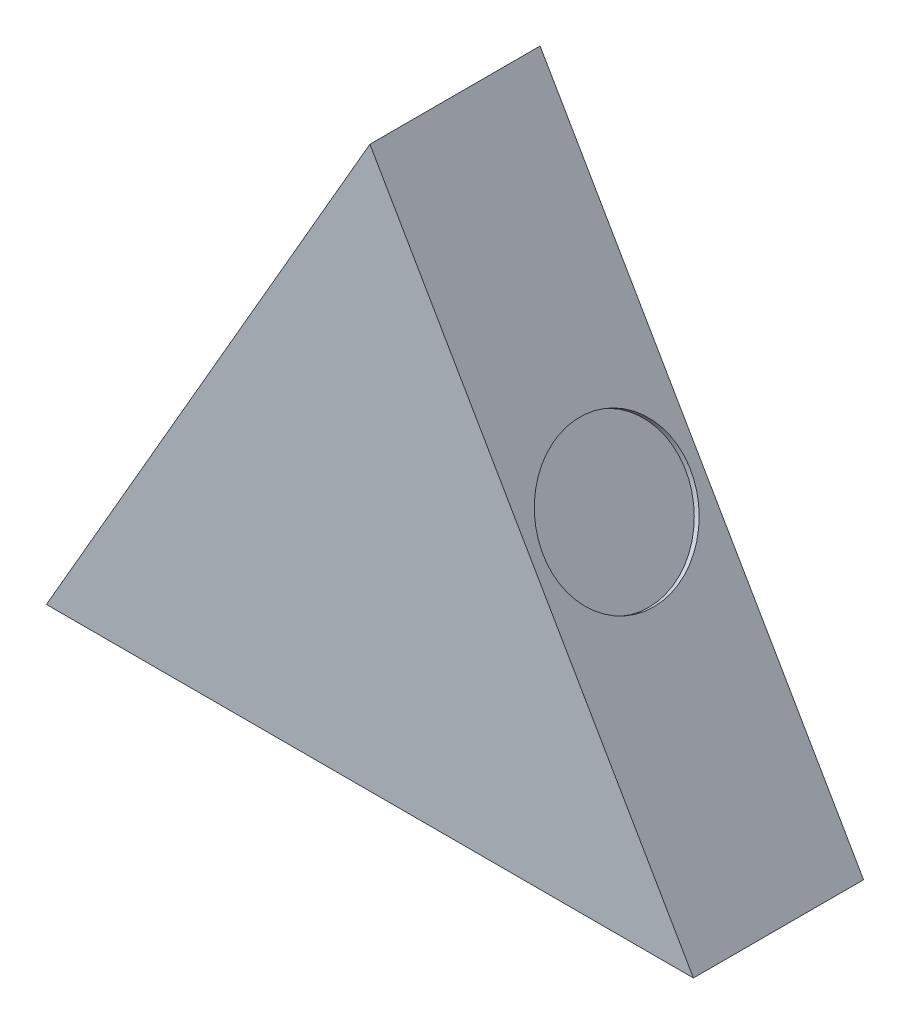
SolidWorks part; units mm, degrees
ref_plane "前视基准面" through (0, 0, 0) normal (0, 0, 1) x (1, 0, 0)
ref_plane "上视基准面" through (0, 0, 0) normal (0, 1, 0) x (1, 0, 0)
ref_plane "右视基准面" through (0, 0, 0) normal (1, 0, 0) x (0, 0, -1)
other "Configuration Table"
sketch "草图1" plane through (0, 0, 0) normal (0, 0, 1) x (1, 0, 0)
  line L0 (0, 0) -> (0, 24.6971) construction
  line L1 (0, 24.6971) -> (-28.5178, -24.6971)
  line L2 (-28.5178, -24.6971) -> (28.5178, -24.6971)
  line L3 (28.5178, -24.6971) -> (0, 24.6971)
  point P4 (0, 0)
extrude "凸台-拉伸2" add sketch "草图1" along normal blind 15
sketch "草图4" plane through (0, 0, 0) normal (0, 0, 1) x (1, 0, 0)
  line L0 (-13.4738, -3.563) -> (-13.4738, -20.063)
  line L1 (-10, -23.5368) -> (10, -23.5368)
  line L2 (13.4738, -3.563) -> (13.4738, -20.063)
  line L3 (-2.3763, 9.7004) -> (-3.4178, 9.4701)
  line L4 (2.3763, 9.7004) -> (3.4178, 9.4701)
  arc A0 (2.3763, 9.7004) -> (-2.3763, 9.7004) centre (0, 6.581) ccw
  arc A1 (-13.4738, -20.063) -> (-10, -23.5368) centre (-10, -20.063) ccw
  arc A2 (10, -23.5368) -> (13.4738, -20.063) centre (10, -20.063) ccw
  arc A3 (13.4738, -3.563) -> (3.4178, 9.4701) centre (0, -3.563) ccw
  arc A4 (-3.4178, 9.4701) -> (-13.4738, -3.563) centre (0, -3.563) ccw
extrude "切除-拉伸2" cut sketch "草图4" along normal blind 13
sketch "草图5" plane through (0, -24.6971, 0) normal (0, -1, 0) x (1, 0, 0)
  line L0 (0, 15) -> (0, 0) construction
  line L1 (-28.5178, 15) -> (28.5178, 15) construction
  circle A0 centre (0, 7.5) radius 6.5
  dimension "D1" = 13
sketch "草图6" plane through (-14.2589, 0, 0) normal (0.866, -0.5, 0) x (0.5, 0.866, 0)
  line L0 (0, 15) -> (0, 0) construction
  circle A0 centre (0, 7.5) radius 6.5
sketch "草图7" plane through (14.2589, 0, 0) normal (-0.866, -0.5, 0) x (0.5, -0.866, 0)
  line L0 (0, 15) -> (0, 0) construction
  circle A0 centre (0, 7.5) radius 6.5
extrude "切除-拉伸3" cut sketch "草图5" against normal blind 0.5
extrude "切除-拉伸5" cut sketch "草图6" along normal blind 0.5
extrude "切除-拉伸8" cut sketch "草图7" along normal blind 0.5
